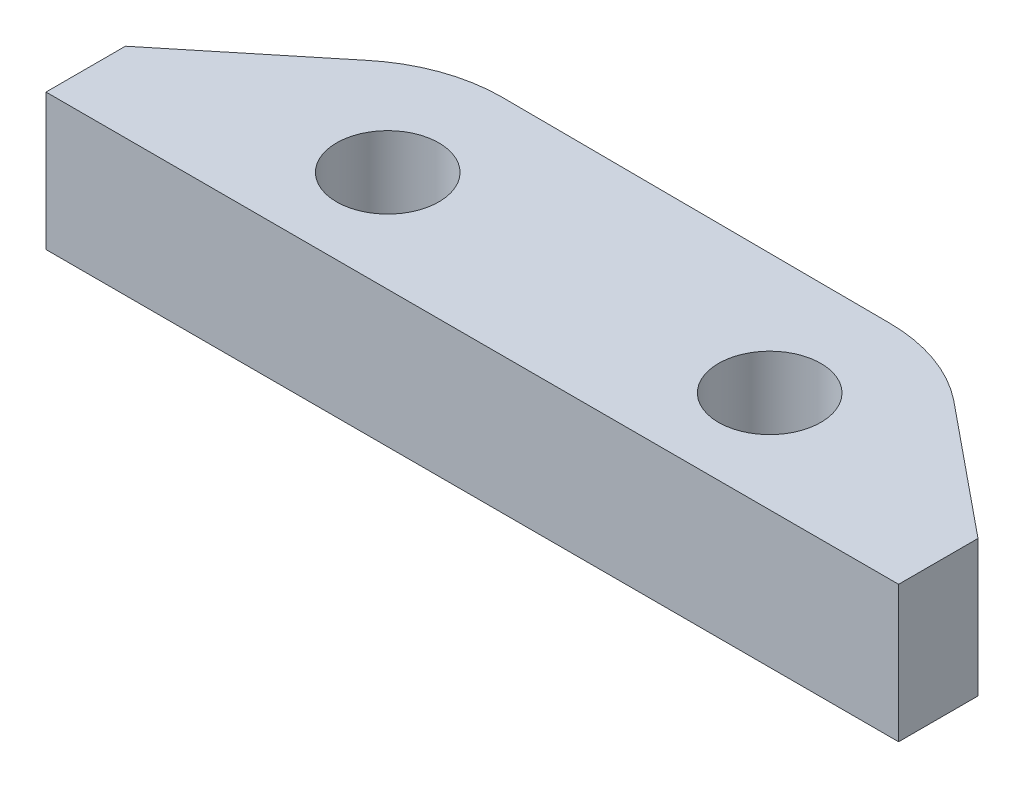
SolidWorks part; units mm, degrees
ref_plane "Alzado" through (0, 0, 0) normal (0, 0, 1) x (1, 0, 0)
ref_plane "Planta" through (0, 0, 0) normal (0, 1, 0) x (1, 0, 0)
ref_plane "Vista lateral" through (0, 0, 0) normal (1, 0, 0) x (0, 0, -1)
sketch "Croquis1" plane through (0, 0, 0) normal (0, 1, 0) x (1, 0, 0)
  line L0 (-12.5, -1.2904) -> (-12.5, -3.6186)
  line L1 (-12.5, -3.6186) -> (12.5, -3.6186)
  line L2 (12.5, -3.6186) -> (12.5, -1.2904)
  line L3 (12.5, -1.2904) -> (8.6279, 1.8683)
  line L4 (5.7199, 2.8818) -> (-5.6874, 2.9379)
  line L5 (-12.5, -1.2904) -> (-8.6279, 1.8683)
  circle A0 centre (-5.45, -0.6486) radius 1.5
  circle A1 centre (5.75, -0.6486) radius 1.5
  arc A2 (-5.6874, 2.9379) -> (-8.6279, 1.8683) centre (-5.6874, -1.6391) ccw
  arc A3 (8.6279, 1.8683) -> (5.7199, 2.8818) centre (5.7199, -1.7967) ccw
extrude "Saliente-Extruir1" add sketch "Croquis1" along normal blind 4
